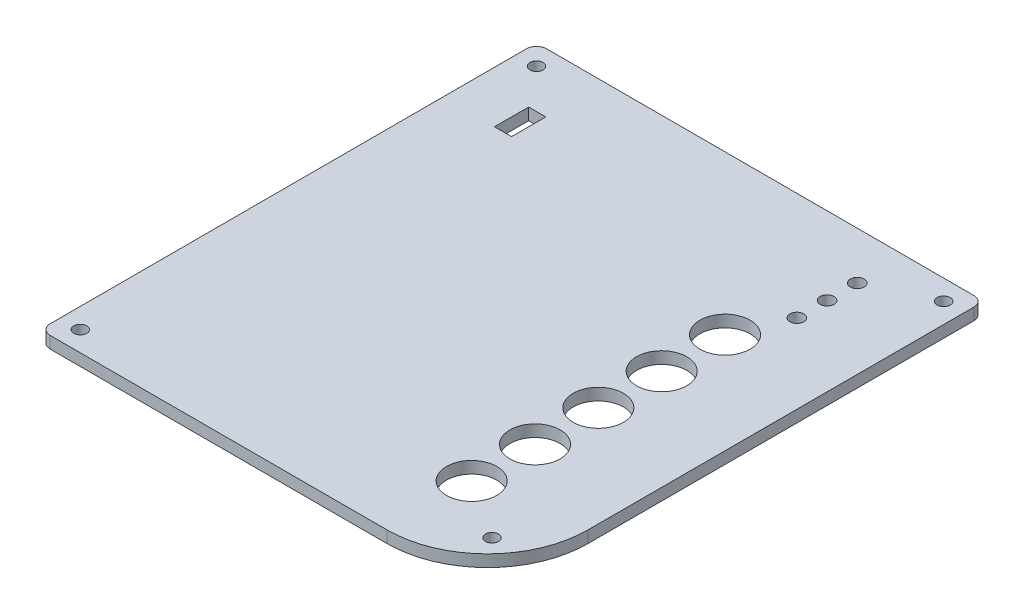
SolidWorks part; units mm, degrees
ref_plane "Front Plane" through (0, 0, 0) normal (0, 0, 1) x (1, 0, 0)
ref_plane "Top Plane" through (0, 0, 0) normal (0, 1, 0) x (1, 0, 0)
ref_plane "Right Plane" through (0, 0, 0) normal (1, 0, 0) x (0, 0, -1)
sketch "Sketch1" plane through (0, 0, 0) normal (0, 1, 0) x (1, 0, 0)
  line L0 (38.2045, 48.03) -> (-54.6555, 48.03) construction
  line L1 (-45.6855, 40.41) -> (29.2345, 40.41) construction
  line L2 (-45.6855, 40.41) -> (-45.6855, -59.5901) construction
  line L3 (-45.6855, -59.5901) -> (29.2345, -59.5901) construction
  line L4 (29.2345, 40.41) -> (29.2345, -59.5901) construction
  line L5 (48.2845, 53.11) -> (-64.7355, 53.11)
  line L6 (48.2845, 53.11) -> (48.2845, -46.8901)
  line L7 (22.8845, -72.2901) -> (-64.7355, -72.2901)
  line L8 (-64.7355, 53.11) -> (-64.7355, -72.2901)
  line L9 (-59.6555, 43.03) -> (-59.6555, -62.2101) construction
  line L10 (22.8845, -67.2101) -> (-54.6555, -67.2101) construction
  line L11 (43.2045, 43.03) -> (43.2045, -46.8901) construction
  line L12 (43.2045, 48.03) -> (-59.6555, 48.03) construction
  line L13 (-59.6555, 48.03) -> (-59.6555, -67.2101) construction
  line L14 (43.2045, 48.03) -> (43.2045, -46.8901) construction
  line L15 (22.8845, -67.2101) -> (-59.6555, -67.2101) construction
  line L16 (-54.6555, 48.03) -> (49945.3445, 48.03) construction
  line L17 (43.2045, 40.4991) -> (43.2045, -49959.5009) construction
  line L18 (-25.2243, -67.2101) -> (-50025.2243, -67.2101) construction
  line L19 (-59.6555, -48.2991) -> (-59.6555, -50048.2991) construction
  arc A0 (22.8845, -72.2901) -> (48.2845, -46.8901) centre (22.8845, -46.8901) ccw
  arc A1 (22.8845, -67.2101) -> (33.9996, -63.9006) centre (22.8845, -46.8901) ccw construction
  circle A2 centre (-59.6555, 48.03) radius 1.65
  arc A3 (-59.6555, 43.03) -> (-54.6555, 48.03) centre (-59.6555, 48.03) ccw construction
  arc A4 (38.2045, 48.03) -> (43.2045, 43.03) centre (43.2045, 48.03) ccw construction
  arc A5 (-54.6555, -67.2101) -> (-59.6555, -62.2101) centre (-59.6555, -67.2101) ccw construction
  arc A6 (40.7175, -56.631) -> (33.9996, -63.9006) centre (37.8809, -60.7485) ccw construction
  arc A7 (22.8845, -67.2101) -> (43.2045, -46.8901) centre (22.8845, -46.8901) ccw construction
  arc A8 (40.7175, -56.631) -> (43.2045, -46.8901) centre (22.8845, -46.8901) ccw construction
  circle A9 centre (43.2045, 48.03) radius 1.65
  circle A10 centre (-59.6555, -67.2101) radius 1.65
  circle A11 centre (37.8809, -60.7485) radius 1.65
  dimension "D3" = 50.8
  dimension "D7" = 25.4
  dimension "D8" = 25.4
  dimension "D9" = 5.08
  dimension "D10" = 3.3
  dimension "D11" = 10
  dimension "D12" = 3.3
  dimension "D13" = 5
  dimension "D14" = 5
  dimension "D15" = 3.3
  dimension "D16" = 3.3
  dimension "D17" = 5
  dimension "D1" = 100.0001
  dimension "D2" = 74.92
  dimension "0.75" = 19.05
  dimension "D4" = 19.05
  dimension "D5" = 12.7
  dimension "D6" = 12.7
extrude "Boss-Extrude3" add sketch "Sketch1" along normal blind 3
sketch "Sketch3" plane through (0, 3, 0) normal (0, 1, 0) x (1, 0, 0)
  line L0 (43.2045, 48.03) -> (-59.6555, 48.03) construction
  line L1 (-8.2255, 48.03) -> (-8.2255, 36.6926) construction
  line L2 (-35.978, 18.03) -> (49964.022, 18.03) construction
  line L3 (48.2845, 53.11) -> (-64.7355, 53.11) construction
  line L4 (-10.3083, 24.03) -> (-10.3083, 21.2203)
  line L5 (-6.1427, 24.03) -> (-6.1427, 21.2203)
  line L6 (-8.2255, 18.03) -> (-8.2255, -49951.97) construction
  line L22 (-59.6555, -67.2101) -> (22.8845, -67.2101)
  line L23 (43.2045, -46.8901) -> (43.2045, 48.03)
  line L24 (43.2045, 48.03) -> (-59.6555, 48.03)
  line L25 (-59.6555, 48.03) -> (-59.6555, -67.2101)
  line L26 (-59.6555, -67.2101) -> (22.8845, -67.2101) construction
  line L27 (43.2045, -46.8901) -> (43.2045, 48.03) construction
  line L28 (43.2045, 48.03) -> (-59.6555, 48.03) construction
  line L29 (-59.6555, 48.03) -> (-59.6555, -67.2101) construction
  arc A0 (-10.3083, 21.2203) -> (-6.1427, 21.2203) centre (-8.2255, 18.03) ccw
  arc A1 (-6.1427, 24.03) -> (-10.3083, 24.03) centre (-8.2255, 24.03) ccw
  arc A3 (22.8845, -67.2101) -> (43.2045, -46.8901) centre (22.8845, -46.8901) ccw
  arc A4 (22.8845, -67.2101) -> (43.2045, -46.8901) centre (22.8845, -46.8901) ccw construction
  point P6 (-8.2255, 48.03)
  dimension "D3" = 7.62
  dimension "D4" = 4.1656
  dimension "D1" = 30
  dimension "D5" = 6
  dimension "D6" = 35.08
  dimension "D2" = 5.08
extrude "Cut-Extrude1" [suppressed] cut sketch "Sketch3" against normal through all
sketch "Sketch4" plane through (0, 3, 0) normal (0, 1, 0) x (1, 0, 0)
  line L4 (48.2845, 53.11) -> (-64.7355, 53.11) construction
  line L5 (-53.7355, 41.11) -> (21.1845, 41.11) construction
  line L6 (-53.7355, 41.11) -> (-53.7355, -58.89) construction
  line L7 (-53.7355, -58.89) -> (21.1845, -58.89) construction
  line L8 (43.2045, -46.8901) -> (43.2045, 48.03)
  line L9 (-59.6555, -67.2101) -> (22.8845, -67.2101)
  line L10 (-59.6555, 48.03) -> (-59.6555, -67.2101)
  line L11 (43.2045, 48.03) -> (-59.6555, 48.03)
  line L12 (43.2045, -46.8901) -> (43.2045, 48.03) construction
  line L13 (-59.6555, -67.2101) -> (22.8845, -67.2101) construction
  line L14 (-59.6555, 48.03) -> (-59.6555, -67.2101) construction
  line L15 (43.2045, 48.03) -> (-59.6555, 48.03) construction
  line L16 (21.1845, 41.11) -> (21.1845, -58.89) construction
  line L17 (-64.7355, 53.11) -> (-64.7355, -72.2901) construction
  circle A1 centre (-49.9355, -6.82) radius 1.75
  arc A2 (22.8845, -67.2101) -> (43.2045, -46.8901) centre (22.8845, -46.8901) ccw
  arc A3 (22.8845, -67.2101) -> (43.2045, -46.8901) centre (22.8845, -46.8901) ccw construction
  circle A4 centre (-6.7555, -41.11) radius 1.75
  circle A5 centre (-10.5655, 33.82) radius 1.75
  dimension "D8" = 17.78
  dimension "D11" = 92.71
  dimension "D12" = 3.5
  dimension "D13" = 3.5
  dimension "D14" = 3.5
  dimension "D2" = 74.92
  dimension "D3" = 100
  dimension "D4" = 12
  dimension "D5" = 11
  dimension "D6" = 52.07
  dimension "D7" = 71.12
  dimension "D9" = 27.94
  dimension "D10" = 31.75
  dimension "D1" = 5.08
extrude "Cut-Extrude2" [suppressed] cut sketch "Sketch4" against normal through all
sketch "Sketch5" plane through (0, 3, 0) normal (0, 1, 0) x (1, 0, 0)
  line L1 (48.2845, 53.11) -> (-64.7355, 53.11) construction
  line L2 (-8.2255, 53.11) -> (-8.2255, -102.4216) construction
  line L3 (-64.7355, -9.59) -> (77.8378, -9.59) construction
  line L4 (-64.7355, 53.11) -> (-64.7355, -72.2901) construction
  circle A0 centre (-8.2255, -9.59) radius 10
  dimension "D1" = 20
extrude "Cut-Extrude3" [suppressed] cut sketch "Sketch5" against normal through all
fillet "Fillet1" radius 2.54 3 edges at (48.2845, 1.5, -53.11) (-64.7355, 1.5, -53.11) (-64.7355, 1.5, 72.2901)
sketch "Sketch6" plane through (0, 3, 0) normal (0, 1, 0) x (1, 0, 0)
  line L1 (48.2845, 53.11) -> (48.2845, -46.8901) construction
  line L2 (48.2845, 53.11) -> (-64.7355, 53.11) construction
  circle A0 centre (22.8845, 13.11) radius 6.35
  circle A1 centre (22.8845, -2.89) radius 6.35
  circle A2 centre (22.8845, -18.89) radius 6.35
  circle A3 centre (22.8845, -34.89) radius 6.35
  circle A4 centre (22.8845, -50.89) radius 6.35
  dimension "D1" = 12.7
  dimension "D2" = 5
  dimension "D3" = 25.4
  dimension "D4" = 40
extrude "Buttons" cut sketch "Sketch6" against normal through all
sketch "Sketch7" plane through (0, 3, 0) normal (0, 1, 0) x (1, 0, 0)
  line L0 (48.2845, 53.11) -> (-64.7355, 53.11) construction
  line L1 (48.2845, 53.11) -> (48.2845, -46.8901) construction
  circle A0 centre (28.2845, 41.11) radius 1.75
  circle A1 centre (28.2845, 33.49) radius 1.75
  circle A2 centre (28.2845, 25.87) radius 1.75
  dimension "D1" = 3.5
  dimension "D3" = 12
  dimension "D4" = 20
  dimension "D2" = 3
extrude "Cut-Extrude5" cut sketch "Sketch7" against normal through all
sketch "Sketch8" plane through (0, 3, 0) normal (0, 1, 0) x (1, 0, 0)
  line L1 (-51.7155, 38.11) -> (-47.3975, 38.11)
  line L2 (-51.7155, 38.11) -> (-51.7155, 29.474)
  line L3 (-51.7155, 29.474) -> (-47.3975, 29.474)
  line L4 (-47.3975, 38.11) -> (-47.3975, 29.474)
  line L5 (48.2845, 53.11) -> (48.2845, -46.8901) construction
  line L6 (48.2845, 53.11) -> (-64.7355, 53.11) construction
  dimension "D1" = 8.636
  dimension "0.17 in" = 4.318
  dimension "D2" = 100
  dimension "D3" = 15
extrude "Cut-Extrude6" cut sketch "Sketch8" against normal through all
